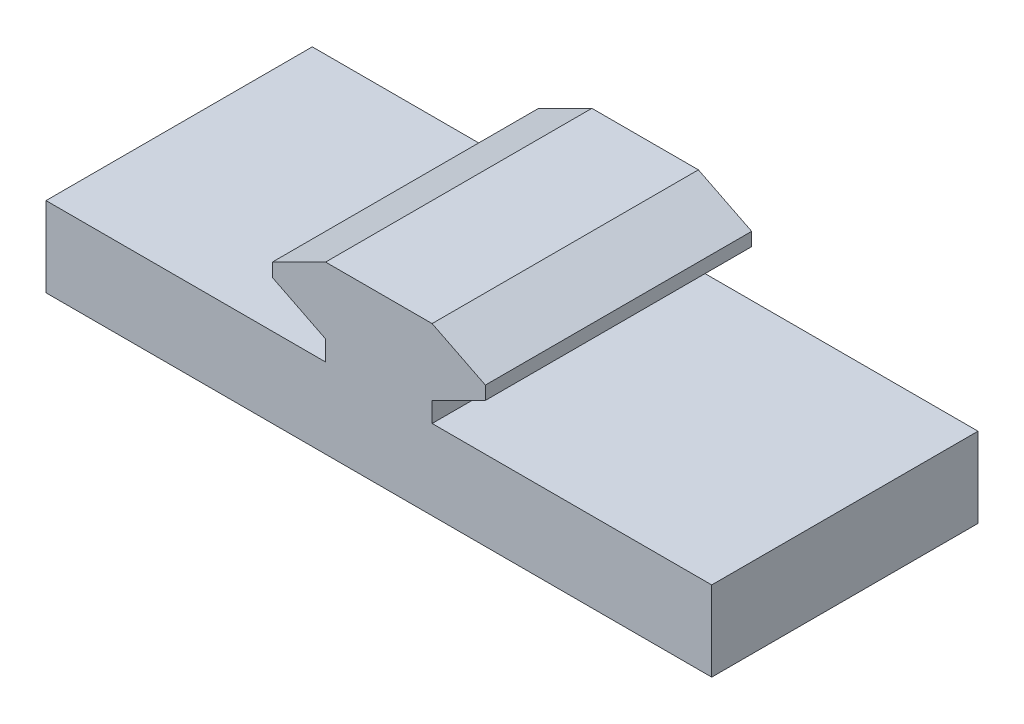
SolidWorks part; units mm, degrees
ref_plane "Спереди" through (0, 0, 0) normal (0, 0, 1) x (1, 0, 0)
ref_plane "Сверху" through (0, 0, 0) normal (0, 1, 0) x (1, 0, 0)
ref_plane "Справа" through (0, 0, 0) normal (1, 0, 0) x (0, 0, -1)
sketch "Эскиз1" plane through (0, 0, 0) normal (0, 0, 1) x (1, 0, 0)
  line L18 (-9.8453, -8.1929) -> (40.1547, -8.1929)
  line L19 (-9.8453, -8.1929) -> (-9.8453, -2.1929)
  line L20 (-9.8453, -2.1929) -> (11.1547, -2.1929)
  line L21 (40.1547, -8.1929) -> (40.1547, -2.1929)
  line L23 (11.1547, -2.1929) -> (11.1547, -0.6929)
  line L25 (19.1547, -2.1929) -> (19.1547, -0.6929)
  line L27 (7.1547, 1.3071) -> (7.1547, 2.3071)
  line L28 (11.1547, 4.3071) -> (19.1547, 4.3071)
  line L29 (23.1547, 1.3071) -> (23.1547, 2.3071)
  line L30 (19.1547, -2.1929) -> (40.1547, -2.1929)
  line L31 (11.1547, -0.6929) -> (7.1547, 1.3071)
  line L32 (19.1547, -0.6929) -> (23.1547, 1.3071)
  line L33 (7.1547, 2.3071) -> (11.1547, 4.3071)
  line L35 (23.1547, 2.3071) -> (19.1547, 4.3071)
  point P13 (23.1547, 1.8071)
  dimension "D1" = 50
  dimension "D2" = 6
  dimension "D3" = 16
  dimension "D4" = 4
  dimension "D5" = 8
  dimension "D6" = 1.5
  dimension "D7" = 1.5
  dimension "D8" = 17
  dimension "D9" = 3.5
  dimension "D10" = 3.5
  dimension "D11" = 4.5
  dimension "D12" = 4.5
  dimension "D13" = 21
  dimension "D14" = 4
extrude "Бобышка-Вытянуть1" add sketch "Эскиз1" along normal blind 20
